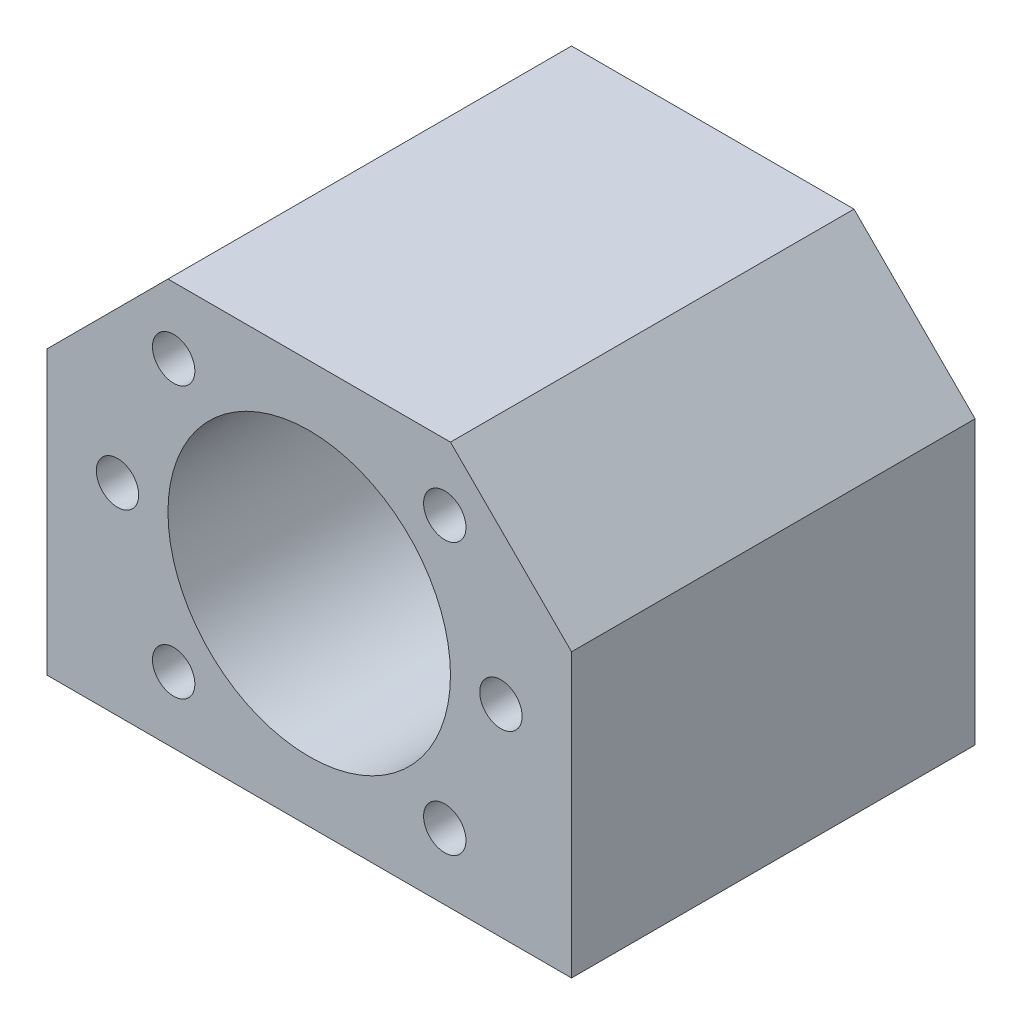
SolidWorks part; units mm, degrees
material "AISI 1045 Acero estirado en frío"
ref_plane "Alzado" through (0, 0, 0) normal (0, 0, 1) x (1, 0, 0)
ref_plane "Planta" through (0, 0, 0) normal (0, 1, 0) x (1, 0, 0)
ref_plane "Vista lateral" through (0, 0, 0) normal (1, 0, 0) x (0, 0, -1)
sketch "Croquis3" plane through (0, 0, 0) normal (0, 0, 1) x (1, 0, 0)
  line L0 (-26, 8) -> (-14, 20)
  line L1 (-26, -20) -> (26, -20)
  line L2 (-26, -20) -> (-26, 8)
  line L3 (-14, 20) -> (14, 20)
  line L4 (26, -20) -> (26, 8)
  line L5 (-26, -20) -> (26, 20) construction
  line L6 (-26, 20) -> (26, -20) construction
  line L7 (26, 8) -> (14, 20)
  point P0 (0, 0)
  dimension "D1" = 52
  dimension "D2" = 40
  dimension "D3" = 12
  dimension "D4" = 12
  dimension "D5" = 12
  dimension "D6" = 12
extrude "Saliente-Extruir2" add sketch "Croquis3" along normal blind 40
ref_plane "Plano2" through (0, 0, 40) normal (0, 0, 1) x (1, 0, 0)
sketch "Croquis4" plane through (0, 0, 40) normal (0, 0, 1) x (1, 0, 0)
  circle A0 centre (0, 0) radius 14
  dimension "D1" = 28
extrude "Cortar-Extruir2" cut sketch "Croquis4" against normal through all
sketch "Croquis5" plane through (0, 0, 40) normal (0, 0, 1) x (1, 0, 0)
  line L0 (0, 22.9891) -> (0, -23.6962) construction
  line L1 (-19, 0) -> (19, 0) construction
  line L2 (0, 0) -> (-13.435, 13.435) construction
  line L3 (0, 0) -> (-13.435, -13.435) construction
  line L4 (0, 0) -> (13.435, -13.435) construction
  line L5 (0, 0) -> (13.435, 13.435) construction
  line L6 (-26, -20) -> (26, -20) construction
  circle A0 centre (0, 0) radius 19
  dimension "D1" = 38
  dimension "D2" = 45
  dimension "D3" = 45
  dimension "D4" = 45
hole_wizard "Taladro roscado M51" positions "Croquis6" profile "Croquis8" tap size "M5" standard "DIN"
sketch "Croquis6" plane through (0, 0, 40) normal (0, 0, 1) x (1, 0, 0)
  point P0 (-13.435, 13.435)
cosmetic thread "Rosca de taladro1" parameters "D1"=40, "D2"=5
sketch "Croquis8" plane through (-13.435, 13.435, 40) normal (1, 0, 0) x (0, -1, 0)
  line L0 (0, 0) -> (0, 16.2618)
  line L1 (0, 16.2618) -> (2.1, 15)
  line L2 (2.1, 15) -> (2.1, 0)
  line L5 (2.1, 0) -> (0, 0)
  line L10 (0, 16.2618) -> (-2.1, 15) construction
  line L11 (0, -6.35) -> (0, 107.95) construction
  dimension "Diámetro de perforador para roscar" = 4.2
  dimension "Profundidad de perforador para roscar" = 15
  dimension "Ángulo de perforador" = 118
hole_wizard "Taladro roscado M52" positions "Croquis11" profile "Croquis12" tap size "M5" standard "DIN"
sketch "Croquis11" plane through (0, 0, 40) normal (0, 0, 1) x (1, 0, 0)
  point P0 (-19, 0)
cosmetic thread "Rosca de taladro2" parameters "D1"=40, "D2"=5
sketch "Croquis12" plane through (-19, 0, 40) normal (1, 0, 0) x (0, -1, 0)
  line L0 (0, 0) -> (0, 16.2618)
  line L1 (0, 16.2618) -> (2.1, 15)
  line L2 (2.1, 15) -> (2.1, 0)
  line L5 (2.1, 0) -> (0, 0)
  line L10 (0, 16.2618) -> (-2.1, 15) construction
  line L11 (0, -6.35) -> (0, 107.95) construction
  dimension "Diámetro de perforador para roscar" = 4.2
  dimension "Profundidad de perforador para roscar" = 15
  dimension "Ángulo de perforador" = 118
hole_wizard "Taladro roscado M53" positions "Croquis13" profile "Croquis14" tap size "M5" standard "DIN"
sketch "Croquis13" plane through (0, 0, 40) normal (0, 0, 1) x (1, 0, 0)
  point P0 (-13.435, -13.435)
  point P3 (13.435, -13.435)
  point P6 (19, 0)
  point P9 (13.435, 13.435)
cosmetic thread "Rosca de taladro3" parameters "D1"=40, "D2"=5
cosmetic thread "Rosca de taladro4" parameters "D1"=40, "D2"=5
cosmetic thread "Rosca de taladro5" parameters "D1"=40, "D2"=5
cosmetic thread "Rosca de taladro6" parameters "D1"=40, "D2"=5
sketch "Croquis14" plane through (-13.435, -13.435, 40) normal (1, 0, 0) x (0, -1, 0)
  line L0 (0, 0) -> (0, 16.2618)
  line L1 (0, 16.2618) -> (2.1, 15)
  line L2 (2.1, 15) -> (2.1, 0)
  line L5 (2.1, 0) -> (0, 0)
  line L10 (0, 16.2618) -> (-2.1, 15) construction
  line L11 (0, -6.35) -> (0, 107.95) construction
  dimension "Diámetro de perforador para roscar" = 4.2
  dimension "Profundidad de perforador para roscar" = 15
  dimension "Ángulo de perforador" = 118
ref_plane "Plano4" through (0, -20, 0) normal (0, 1, 0) x (1, 0, 0)
sketch "Croquis20" plane through (0, -20, 0) normal (0, 1, 0) x (1, 0, 0)
  line L0 (-26, 0) -> (-20, 0) construction
  line L1 (-26, 0) -> (26, 0) construction
  line L2 (26, 0) -> (20, 0) construction
  line L3 (-20, 0) -> (-20, -40) construction
  line L4 (-26, -40) -> (26, -40) construction
  line L5 (20, 0) -> (20, -40) construction
  line L6 (-26, 0) -> (-26, -8) construction
  line L7 (-26, -40) -> (-26, 0) construction
  line L8 (-26, -8) -> (-20, -8) construction
  line L9 (-20, -8) -> (20, -8) construction
  line L10 (-26, -8) -> (-26, -32) construction
  line L11 (-26, -32) -> (-20, -32) construction
  line L12 (-20, -32) -> (20, -32) construction
  circle A0 centre (-20, -32) radius 2.1
  circle A1 centre (20, -32) radius 2.1
  circle A2 centre (-20, -8) radius 2.1
  circle A3 centre (20, -8) radius 2.1
  dimension "D5" = 4.2
  dimension "D6" = 4.2
  dimension "D7" = 4.2
  dimension "D8" = 4.2
  dimension "D1" = 6
  dimension "D2" = 6
  dimension "D3" = 8
  dimension "D4" = 24
extrude "Cortar-Extruir3" cut sketch "Croquis20" along normal blind 15
